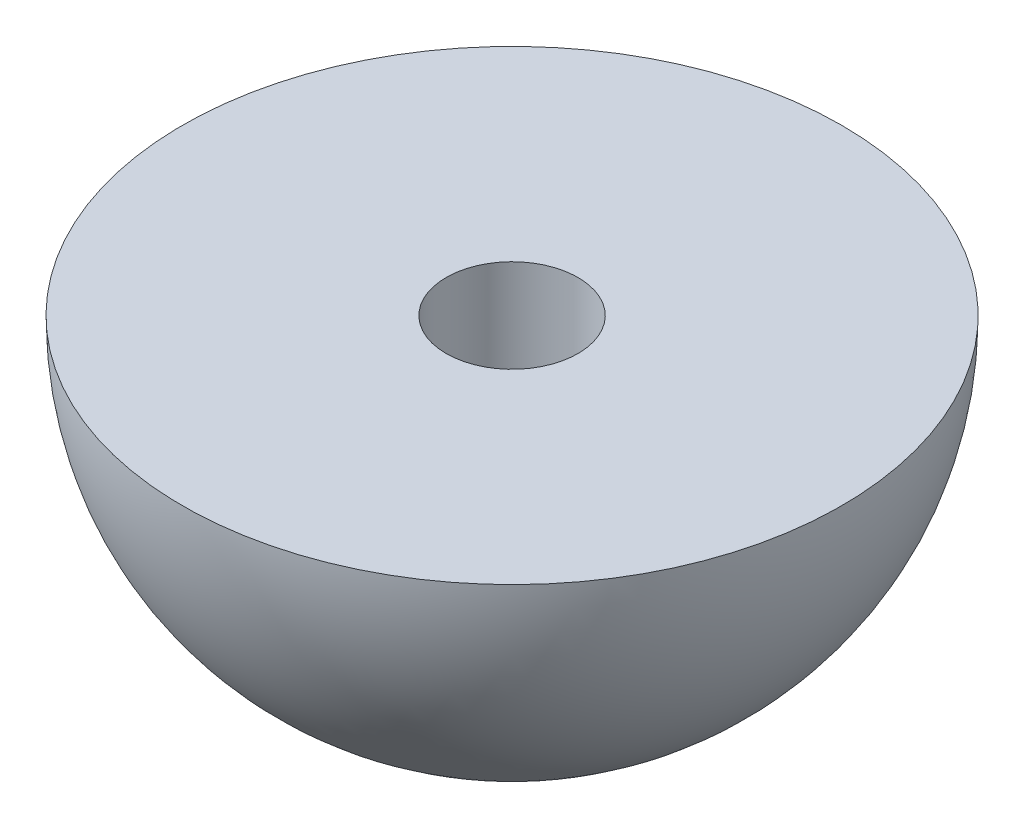
SolidWorks part; units mm, degrees
ref_plane "正面" through (0, 0, 0) normal (0, 0, 1) x (1, 0, 0)
ref_plane "平面" through (0, 0, 0) normal (0, 1, 0) x (1, 0, 0)
ref_plane "右側面" through (0, 0, 0) normal (1, 0, 0) x (0, 0, -1)
sketch "ｽｹｯﾁ1" plane through (0, 0, 0) normal (0, 0, 1) x (1, 0, 0)
  line L0 (0, -8) -> (0, 0)
  line L1 (0, 0) -> (8, 0)
  arc A0 (8, 0) -> (0, -8) centre (0, 0) cw
revolve "回転1" add sketch "ｽｹｯﾁ1" angle 360 about L0
sketch "ｽｹｯﾁ2" plane through (0, 0, 0) normal (0, 1, 0) x (1, 0, 0)
  circle A0 centre (0, 0) radius 1.6
extrude "ｶｯﾄ - 押し出し1" cut sketch "ｽｹｯﾁ2" against normal through all
